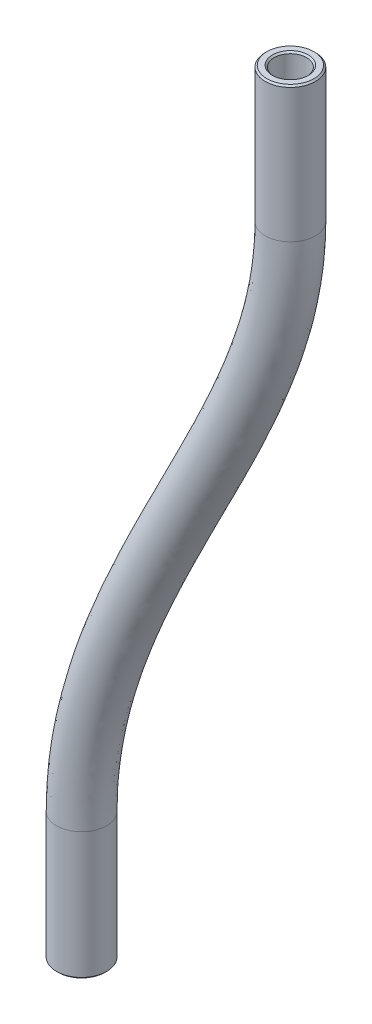
SolidWorks part; units mm, degrees
ref_plane "Front Plane" through (0, 0, 0) normal (0, 0, 1) x (1, 0, 0)
ref_plane "Top Plane" through (0, 0, 0) normal (0, 1, 0) x (1, 0, 0)
ref_plane "Right Plane" through (0, 0, 0) normal (1, 0, 0) x (0, 0, -1)
sketch3d "3DSketch1"
  line L0 (-150.0853, -93.2823, 9.525) -> (-150.0853, -103.4823, 9.525)
  line L1 (-135.8474, -35.8, 7.0985) -> (-135.8474, -46.6, 7.0985)
  spline S0 degree 3 poles (-135.8474, -46.6, 7.0985) (-135.8474, -54.0926, 7.0985) (-142.9663, -69.3235, 8.3117) (-150.0853, -84.4064, 9.525) (-150.0853, -93.2823, 9.525) knots 0 0 0 0 0.459991 1 1 1 1
sketch "Sketch1" plane through (0, -95.3823, 0) normal (0, 1, 0) x (1, 0, 0)
  circle A0 centre (-150.0853, -9.525) radius 2
  circle A1 centre (-150.0853, -9.525) radius 3.6 construction
  circle A2 centre (-150.0853, -9.525) radius 1.3
  dimension "D1" = 4
  dimension "D2" = 2.6
sweep "Sweep1" add profiles "Sketch1" path "3DSketch1"
chamfer "Chamfer1" distance 0.127 angle 45 4 edges at (-150.0853, -103.4823, 11.525) (-150.0853, -103.4823, 10.825) (-135.8474, -35.8, 9.0985) (-135.8474, -35.8, 8.3985)
